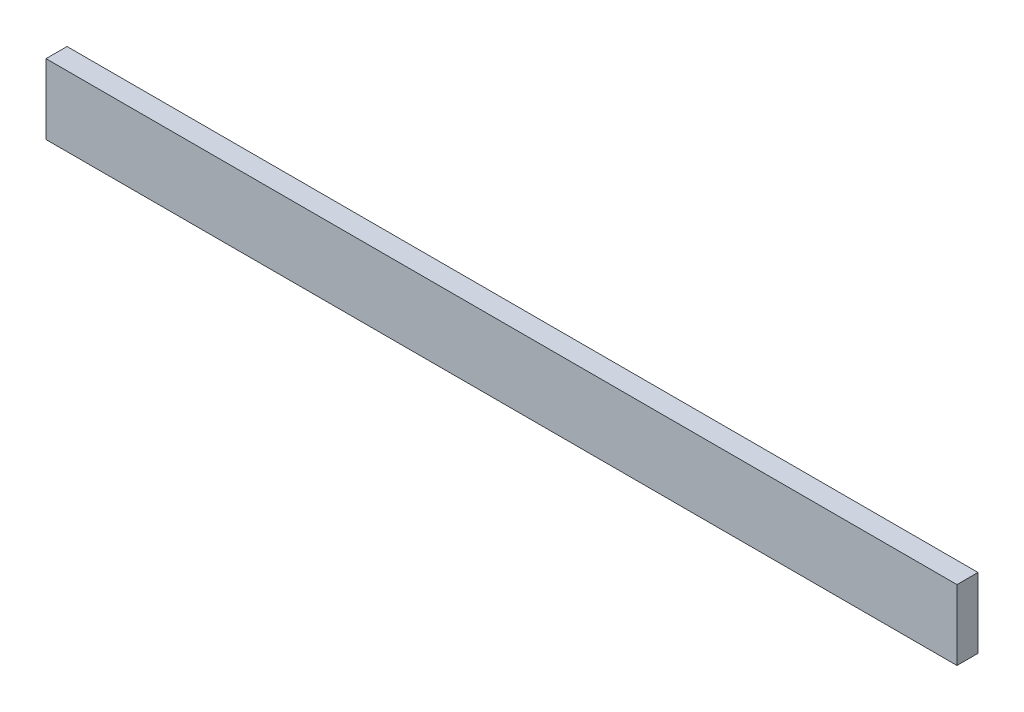
SolidWorks part; units mm, degrees
ref_plane "Plano frontal" through (0, 0, 0) normal (0, 0, 1) x (1, 0, 0)
ref_plane "Plano superior" through (0, 0, 0) normal (0, 1, 0) x (1, 0, 0)
ref_plane "Plano direito" through (0, 0, 0) normal (1, 0, 0) x (0, 0, -1)
sketch "Esboço1" plane through (0, 0, 0) normal (0, 0, 1) x (1, 0, 0)
  line L1 (-72.1079, 0) -> (57.8921, 0)
  line L2 (-72.1079, 0) -> (-72.1079, -10)
  line L3 (-72.1079, -10) -> (57.8921, -10)
  line L4 (57.8921, 0) -> (57.8921, -10)
  dimension "D1" = 130
  dimension "D2" = 10
extrude "Ressalto-extrusão3" add sketch "Esboço1" along normal blind 3
